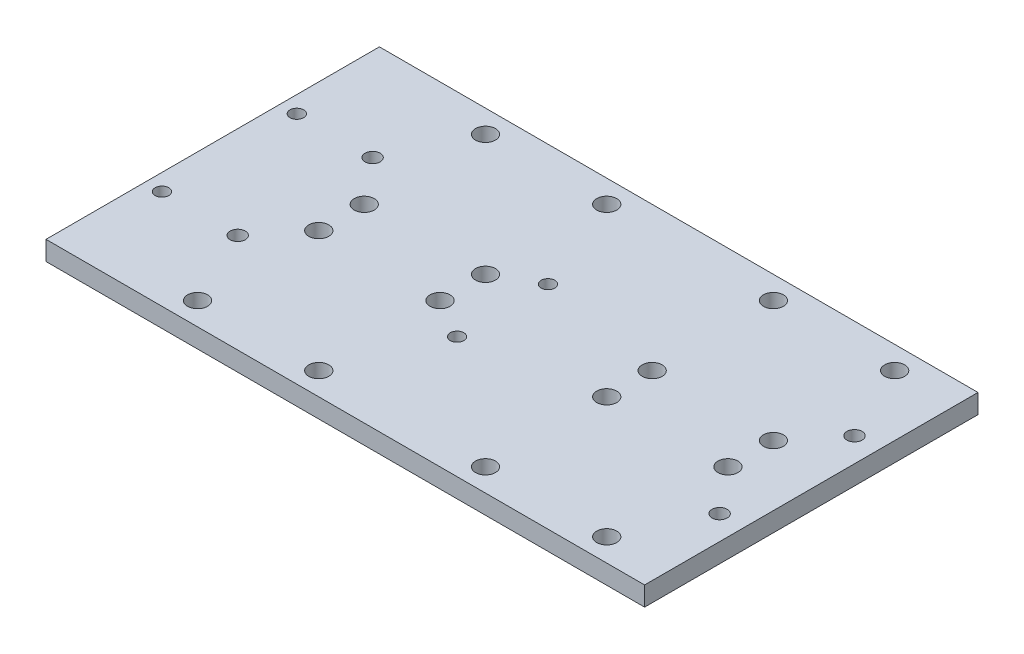
SolidWorks part; units mm, degrees
material "1060 Alloy"
ref_plane "Front Plane" through (0, 0, 0) normal (0, 0, 1) x (1, 0, 0)
ref_plane "Top Plane" through (0, 0, 0) normal (0, 1, 0) x (1, 0, 0)
ref_plane "Right Plane" through (0, 0, 0) normal (1, 0, 0) x (0, 0, -1)
sketch "Sketch1" plane through (0, 0, 0) normal (0, 1, 0) x (1, 0, 0)
  line L1 (-100, -55) -> (100, -55)
  line L2 (-100, -55) -> (-100, 55)
  line L3 (-100, 55) -> (100, 55)
  line L4 (100, -55) -> (100, 55)
  line L5 (-100, -55) -> (100, 55) construction
  line L6 (-100, 55) -> (100, -55) construction
  point P0 (0, 0)
  dimension "D1" = 110
  dimension "D2" = 200
extrude "Boss-Extrude1" add sketch "Sketch1" along normal blind 6.35
sketch "LB Holes" plane through (0, 6.35, 0) normal (0, 1, 0) x (1, 0, 0)
  line L0 (0, 0) -> (0, 55) construction
  line L1 (100, 55) -> (-100, 55) construction
  line L2 (0, 0) -> (-100, 0) construction
  line L3 (-100, 55) -> (-100, -55) construction
  line L4 (-47.5, 0) -> (-47.5, 55) construction
  line L5 (-47.5, 27.5) -> (-100, 27.5) construction
  line L6 (-10, 27.5) -> (10, 27.5)
  line L7 (-18, 0) -> (-18, 55) construction
  line L8 (-72, 0) -> (-72, 55) construction
  point P12 (-67.5, 47.5)
  point P13 (-27.5, 47.5)
  point P16 (-27.5, 7.5)
  point P17 (-67.5, 7.5)
  point P19 (-67.5, -7.5)
  point P20 (-27.5, -7.5)
  point P21 (-27.5, -47.5)
  point P22 (-67.5, -47.5)
  point P24 (27.5, -47.5)
  point P25 (67.5, -47.5)
  point P26 (27.5, -7.5)
  point P27 (67.5, -7.5)
  point P28 (67.5, 7.5)
  point P29 (27.5, 7.5)
  point P30 (27.5, 47.5)
  point P31 (67.5, 47.5)
  point P36 (0, 27.5)
  dimension "D1" = 47.5
  dimension "D2" = 20
  dimension "D3" = 20
  dimension "D4" = 20
  dimension "D5" = 54
hole_wizard "M6 Clearance Hole1" positions "3DSketch1" profile "Sketch3" hole size "M6" standard "ANSI Metric"
sketch3d "3DSketch1"
  point P0 (-67.5, 6.35, -47.5)
  point P3 (-27.5, 6.35, -47.5)
  point P6 (-27.5, 6.35, -7.5)
  point P9 (-67.5, 6.35, -7.5)
  point P12 (-67.5, 6.35, 7.5)
  point P15 (-27.5, 6.35, 7.5)
  point P18 (-27.5, 6.35, 47.5)
  point P21 (-67.5, 6.35, 47.5)
  point P24 (27.5, 6.35, 47.5)
  point P27 (27.5, 6.35, 7.5)
  point P30 (27.5, 6.35, -7.5)
  point P33 (27.5, 6.35, -47.5)
  point P36 (67.5, 6.35, -47.5)
  point P39 (67.5, 6.35, -7.5)
  point P42 (67.5, 6.35, 7.5)
  point P45 (67.5, 6.35, 47.5)
sketch "Sketch3" plane through (-67.5, 6.35, -47.5) normal (1, 0, 0) x (0, 0, 1)
  line L0 (0, 0) -> (0, 14.3828)
  line L1 (0, 14.3828) -> (3.3, 12.4)
  line L2 (3.3, 12.4) -> (3.3, 0)
  line L5 (3.3, 0) -> (0, 0)
  line L10 (0, 14.3828) -> (-3.3, 12.4) construction
  line L11 (0, -6.35) -> (0, 107.95) construction
  dimension "Hole Dia." = 6.6
  dimension "Hole Depth" = 12.4
  dimension "Drill Angle" = 118
sketch "Extendo" plane through (0, 6.35, 0) normal (0, 1, 0) x (1, 0, 0)
  line L0 (-47.5, 0) -> (-47.5, 55) construction
  line L1 (0, 0) -> (0, 55) construction
  line L2 (0, 0) -> (-100, 0) construction
  line L3 (-47.5, 0) -> (-47.5, 55) construction
  line L4 (0, 0) -> (0, 55) construction
  line L5 (0, 0) -> (-100, 0) construction
  line L6 (-74.5, 0) -> (-74.5, 55) construction
  line L7 (100, 55) -> (-100, 55) construction
  line L8 (-79.5, 0) -> (-79.5, 55) construction
  line L10 (-100, 55) -> (-110, 55)
  line L11 (-100, 55) -> (-100, -55)
  line L12 (-100, -55) -> (-110, -55)
  line L13 (-110, 55) -> (-110, -55)
  point P11 (-79.5, 22.25)
  point P12 (-79.5, -22.25)
  point P14 (79.5, 22.25)
  point P15 (79.5, -22.25)
  dimension "D1" = 27
  dimension "D2" = 5
  dimension "D3" = 22.25
  dimension "D4" = 10
  dimension "D5" = 110
extrude "Boss-Extrude2" add sketch "Extendo" against normal blind 6.35
sketch "RB Holes" plane through (0, 6.35, 0) normal (0, 1, 0) x (1, 0, 0)
  line L0 (-79.5, 0) -> (-79.5, 55) construction
  line L1 (-79.5, 0) -> (-79.5, 55)
  point P0 (79.5, 22.25)
  point P2 (79.5, -22.25)
  point P4 (-79.5, -22.25)
  point P6 (-79.5, 22.25)
hole_wizard "M6x1.0 Tapped Hole2" positions "3DSketch4" profile "Sketch15" tap size "M6x1.0" standard "ANSI Metric"
sketch3d "3DSketch4"
  point P0 (-79.5, 6.35, -22.25)
  point P3 (-79.5, 6.35, 22.25)
  point P6 (79.5, 6.35, 22.25)
  point P9 (79.5, 6.35, -22.25)
sketch "Sketch15" plane through (-79.5, 6.35, -22.25) normal (1, 0, 0) x (0, 0, 1)
  line L0 (0, 0) -> (0, 16.5022)
  line L1 (0, 16.5022) -> (2.5, 15)
  line L2 (2.5, 15) -> (2.5, 0)
  line L5 (2.5, 0) -> (0, 0)
  line L10 (0, 16.5022) -> (-2.5, 15) construction
  line L11 (0, -6.35) -> (0, 107.95) construction
  dimension "Tap Drill Dia." = 5
  dimension "Tap Drill Depth" = 15
  dimension "Drill Angle" = 118
cosmetic thread "Hole Thread9" parameters "D1"=6.35, "D2"=6
cosmetic thread "Hole Thread10" parameters "D1"=6.35, "D2"=6
cosmetic thread "Hole Thread11" parameters "D1"=6.35, "D2"=6
cosmetic thread "Hole Thread12" parameters "D1"=6.35, "D2"=6
sketch "EM Holes" plane through (0, 6.35, 0) normal (0, 1, 0) x (1, 0, 0)
  line L0 (-79.5, 0) -> (-79.5, 55) construction
  line L1 (0, 0) -> (-100, 0) construction
  line L2 (0, 0) -> (0, 55) construction
  line L3 (-79.5, 0) -> (-79.5, 55) construction
  line L4 (0, 0) -> (-100, 0) construction
  line L5 (0, 0) -> (0, 55) construction
  line L6 (-104.5, 0) -> (-104.5, 55) construction
  line L7 (100, 55) -> (-110, 55) construction
  point P9 (-104.5, 22.25)
  point P10 (-104.5, -22.25)
  dimension "D1" = 25
  dimension "D2" = 22.25
hole_wizard "M4 Clearance Hole2" positions "3DSketch5" profile "Sketch17" hole size "M4" standard "ANSI Metric"
sketch3d "3DSketch5"
  point P0 (-104.5, 6.35, -22.25)
  point P3 (-104.5, 6.35, 22.25)
sketch "Sketch17" plane through (-104.5, 6.35, -22.25) normal (1, 0, 0) x (0, 0, 1)
  line L0 (0, 0) -> (0, 16.3519)
  line L1 (0, 16.3519) -> (2.25, 15)
  line L2 (2.25, 15) -> (2.25, 0)
  line L5 (2.25, 0) -> (0, 0)
  line L10 (0, 16.3519) -> (-2.25, 15) construction
  line L11 (0, -6.35) -> (0, 107.95) construction
  dimension "Hole Dia." = 4.5
  dimension "Hole Depth" = 15
  dimension "Drill Angle" = 118
sketch "BM Holes" plane through (0, 6.35, 0) normal (0, 1, 0) x (1, 0, 0)
  line L0 (-14.375, 0) -> (-14.375, 55) construction
  line L1 (100, 55) -> (-110, 55) construction
  line L2 (0, 0) -> (-100, 0) construction
  line L4 (0, 0) -> (-14.375, 0) construction
  point P4 (-14.375, 15)
  point P9 (-14.375, -15)
  dimension "D1" = 14.375
  dimension "D2" = 15
hole_wizard "M4 Clearance Hole3" positions "3DSketch6" profile "Sketch19" hole size "M4" standard "ANSI Metric"
sketch3d "3DSketch6"
  point P0 (-14.375, 6.35, -15)
  point P3 (-14.375, 6.35, 15)
sketch "Sketch19" plane through (-14.375, 6.35, -15) normal (1, 0, 0) x (0, 0, 1)
  line L0 (0, 0) -> (0, 16.3519)
  line L1 (0, 16.3519) -> (2.25, 15)
  line L2 (2.25, 15) -> (2.25, 0)
  line L5 (2.25, 0) -> (0, 0)
  line L10 (0, 16.3519) -> (-2.25, 15) construction
  line L11 (0, -6.35) -> (0, 107.95) construction
  dimension "Hole Dia." = 4.5
  dimension "Hole Depth" = 15
  dimension "Drill Angle" = 118
sketch "Sketch20" plane through (0, 6.35, 0) normal (0, 1, 0) x (1, 0, 0)
  line L0 (-110, -55) -> (100, -55) construction
  line L1 (100, 55) -> (87.5, 55)
  line L2 (100, 55) -> (100, -55)
  line L3 (100, -55) -> (87.5, -55)
  line L4 (87.5, 55) -> (87.5, -55)
  dimension "D1" = 12.5
extrude "Cut-Extrude1" cut sketch "Sketch20" against normal blind 6.35
